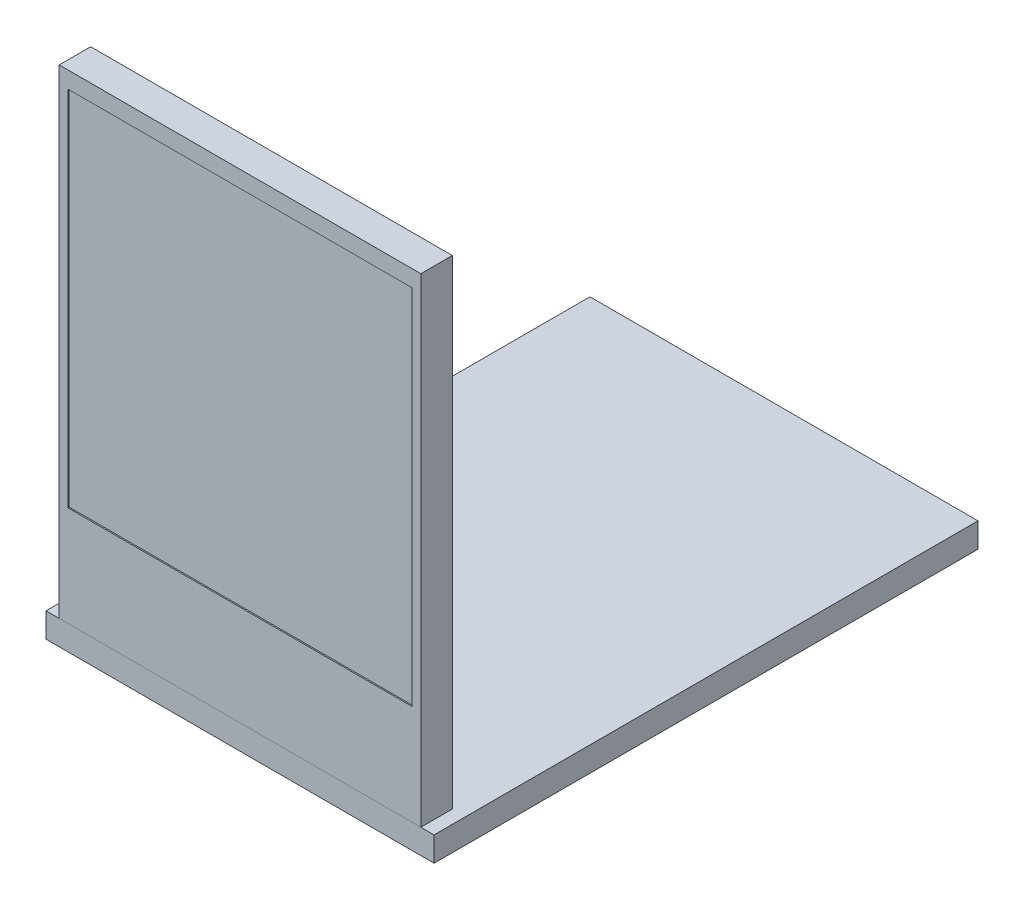
SolidWorks part; units mm, degrees
ref_plane "Front Plane" through (0, 0, 0) normal (0, 0, 1) x (1, 0, 0)
ref_plane "Top Plane" through (0, 0, 0) normal (0, 1, 0) x (1, 0, 0)
ref_plane "Right Plane" through (0, 0, 0) normal (1, 0, 0) x (0, 0, -1)
sketch "Sketch1" plane through (0, 0, 0) normal (0, 1, 0) x (1, 0, 0)
  line L1 (-15.785, 44.25) -> (15.785, 44.25)
  line L2 (-15.785, 44.25) -> (-15.785, 0)
  line L3 (-15.785, 0) -> (15.785, 0)
  line L4 (15.785, 44.25) -> (15.785, 0)
  line L5 (-15.785, 44.25) -> (15.785, 0) construction
  line L6 (-15.785, 0) -> (15.785, 44.25) construction
  point P0 (0, 22.125)
  dimension "D1" = 31.57
  dimension "D2" = 44.25
extrude "Boss-Extrude1" add sketch "Sketch1" against normal blind 2
sketch "Sketch2" plane through (0, 0, 0) normal (0, 0, 1) x (1, 0, 0)
  line L0 (-15.785, -2) -> (15.785, -2) construction
  line L1 (-14.71, 39) -> (14.71, 39)
  line L2 (-14.71, 39) -> (-14.71, 0)
  line L3 (-14.71, 0) -> (14.71, 0)
  line L4 (14.71, 39) -> (14.71, 0)
  line L5 (-14.71, 39) -> (14.71, 0) construction
  line L6 (-14.71, 0) -> (14.71, 39) construction
  line L7 (-15.785, 0) -> (15.785, 0) construction
  point P0 (0, 19.5)
  dimension "D1" = 41
  dimension "D2" = 29.42
extrude "Boss-Extrude2" add sketch "Sketch2" against normal blind 2.56 separate body
sketch "Sketch3" plane through (0, 0, 0) normal (0, 0, 1) x (1, 0, 0)
  line L0 (0, 0) -> (0, 39.6936) construction
  line L1 (14.71, 39) -> (-14.71, 39) construction
  line L2 (-14, 37.65) -> (14, 37.65)
  line L3 (-14, 37.65) -> (-14, 8.15)
  line L4 (-14, 8.15) -> (14, 8.15)
  line L5 (14, 37.65) -> (14, 8.15)
  line L6 (-14, 37.65) -> (14, 8.15) construction
  line L7 (-14, 8.15) -> (14, 37.65) construction
  point P3 (0, 22.9)
  dimension "D1" = 28
  dimension "D2" = 1.35
  dimension "D3" = 29.5
extrude "Cut-Extrude1" cut sketch "Sketch3" against normal blind 0.1
